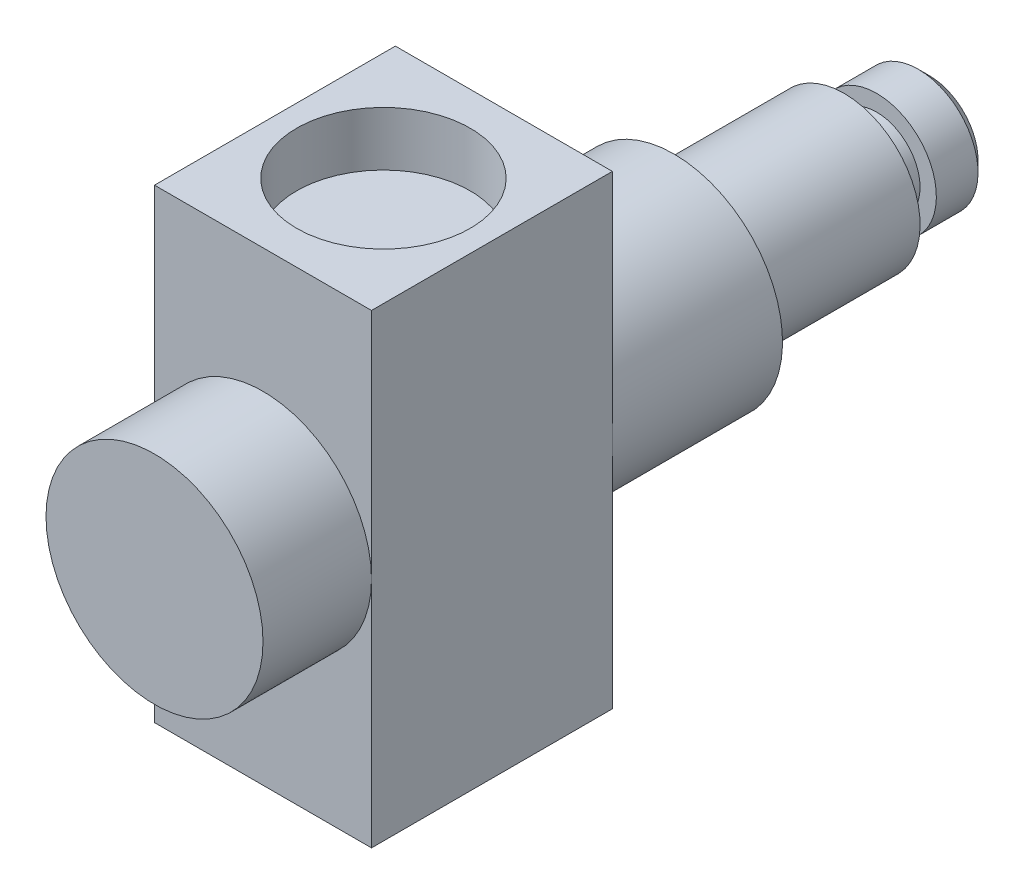
SolidWorks part; units mm, degrees
material "Free-Cutting Brass, UNS C36000"
ref_plane "Front Plane" through (0, 0, 0) normal (0, 0, 1) x (1, 0, 0)
ref_plane "Top Plane" through (0, 0, 0) normal (0, 1, 0) x (1, 0, 0)
ref_plane "Right Plane" through (0, 0, 0) normal (1, 0, 0) x (0, 0, -1)
sketch "Sketch3" plane through (0, 0, 0) normal (1, 0, 0) x (0, 0, -1)
  line L1 (-11.1, 21.45) -> (11.1, 21.45)
  line L2 (-11.1, 21.45) -> (-11.1, -21.45)
  line L3 (-11.1, -21.45) -> (11.1, -21.45)
  line L4 (11.1, 21.45) -> (11.1, -21.45)
  line L5 (-11.1, 21.45) -> (11.1, -21.45) construction
  line L6 (-11.1, -21.45) -> (11.1, 21.45) construction
  point P0 (0, 0)
  dimension "D1" = 42.9
  dimension "D2" = 22.2
extrude "Boss-Extrude2" add sketch "Sketch3" along normal blind 20
sketch "Sketch4" plane through (0, 21.45, 0) normal (0, 1, 0) x (1, 0, 0)
  circle A0 centre (10, 0) radius 8
  dimension "D1" = 16
extrude "Cut-Extrude1" cut sketch "Sketch4" against normal blind 5
sketch "Sketch5" plane through (0, -21.45, 0) normal (0, -1, 0) x (1, 0, 0)
  circle A0 centre (10, 0) radius 8
  dimension "D1" = 16
extrude "Cut-Extrude2" cut sketch "Sketch5" against normal blind 5
sketch "Sketch11" plane through (0, 0, -11.1) normal (0, 0, -1) x (-1, 0, 0)
  line L0 (0, 0) -> (-20, 0) construction
  line L1 (-20, -21.45) -> (-20, 21.45) construction
  circle A0 centre (-10, 0) radius 10
  dimension "D1" = 20
extrude "Boss-Extrude3" add sketch "Sketch11" along normal blind 39.2
sketch "Sketch13" plane through (0, 0, -50.3) normal (0, 0, -1) x (-1, 0, 0)
  circle A0 centre (-10, 0) radius 7
  circle A1 centre (-10, 0) radius 10
  dimension "D1" = 14
  dimension "D2" = 20
extrude "Cut-Extrude5" cut sketch "Sketch13" against normal blind 23.52
sketch "Sketch14" plane through (0, 0, -50.3) normal (0, 0, -1) x (-1, 0, 0)
  circle A0 centre (-10, 0) radius 5.5
  circle A1 centre (-10, 0) radius 7
  dimension "D1" = 11
  dimension "D2" = 14
extrude "Cut-Extrude6" cut sketch "Sketch14" against normal blind 7.84
chamfer "Chamfer2" distance 1 angle 45 1 edges at (10, 5.5, -50.3)
sketch "Sketch15" plane through (0, 0, -42.46) normal (0, 0, -1) x (-1, 0, 0)
  circle A0 centre (-10, 0) radius 5.5
  circle A1 centre (-10, 0) radius 4
  dimension "D1" = 11
  dimension "D2" = 8
extrude "Cut-Extrude7" cut sketch "Sketch15" along normal blind 3
sketch "Sketch16" plane through (0, 0, 11.1) normal (0, 0, 1) x (1, 0, 0)
  line L0 (0, 0) -> (20, 0) construction
  line L1 (20, 21.45) -> (20, -21.45) construction
  circle A0 centre (10, 0) radius 10
  dimension "D1" = 20
extrude "Boss-Extrude4" add sketch "Sketch16" along normal blind 10 contours A0
